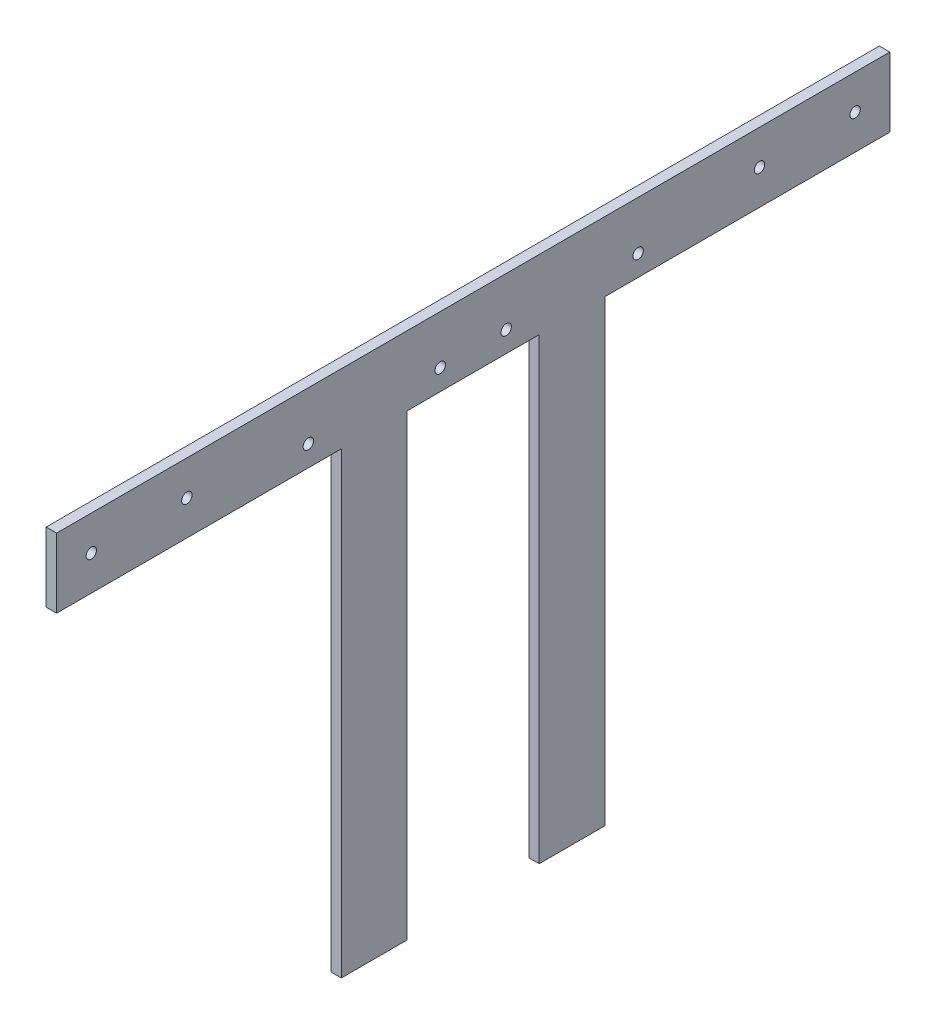
SolidWorks part; units mm, degrees
ref_plane "前视基准面" through (0, 0, 0) normal (0, 0, 1) x (1, 0, 0)
ref_plane "上视基准面" through (0, 0, 0) normal (0, 1, 0) x (1, 0, 0)
ref_plane "右视基准面" through (0, 0, 0) normal (1, 0, 0) x (0, 0, -1)
other "Configuration Table"
sketch "草图1" plane through (0, 0, 0) normal (1, 0, 0) x (0, 0, -1)
  line L0 (15, 0) -> (15, -20) construction
  line L1 (0, 0) -> (240, 0)
  line L2 (0, 0) -> (0, -20)
  line L3 (0, -20) -> (82, -20)
  line L4 (240, 0) -> (240, -20)
  line L5 (65, 0) -> (65, -20) construction
  line L6 (120, -20) -> (120, 0) construction
  line L7 (0, -10) -> (15, -10) construction
  line L8 (158, -152) -> (139, -152)
  line L10 (82, -20) -> (82, -152)
  line L11 (82, -152) -> (101, -152)
  line L12 (101, -20) -> (101, -152)
  line L13 (139, -20) -> (139, -152)
  line L15 (158, -20) -> (158, -152)
  line L16 (101, -20) -> (139, -20)
  line L17 (158, -20) -> (240, -20)
  line L18 (27.52, 0) -> (27.52, -20) construction
  circle A0 centre (72.5, -14) radius 1.5
  circle A1 centre (110.5, -14) radius 1.5
  circle A2 centre (129.5, -14) radius 1.5
  circle A3 centre (167.5, -14) radius 1.5
  circle A4 centre (10, -10) radius 1.5
  circle A5 centre (230, -10) radius 1.5
  circle A6 centre (37.52, -10) radius 1.5
  circle A7 centre (202.48, -10) radius 1.5
  point P35 (27.52, -10)
  dimension "D6" = 3
  dimension "D9" = 3
  dimension "D11" = 3
  dimension "D18" = 3
  dimension "D1" = 240
  dimension "D2" = 20
  dimension "D3" = 15
  dimension "D4" = 50
  dimension "D5" = 6
  dimension "D7" = 7.5
  dimension "D8" = 6
  dimension "D10" = 38
  dimension "D12" = 10
  dimension "D13" = 132
  dimension "D14" = 19
  dimension "D15" = 17
  dimension "D16" = 92.48
  dimension "D17" = 10
extrude "凸台-拉伸1" add sketch "草图1" along normal blind 3
